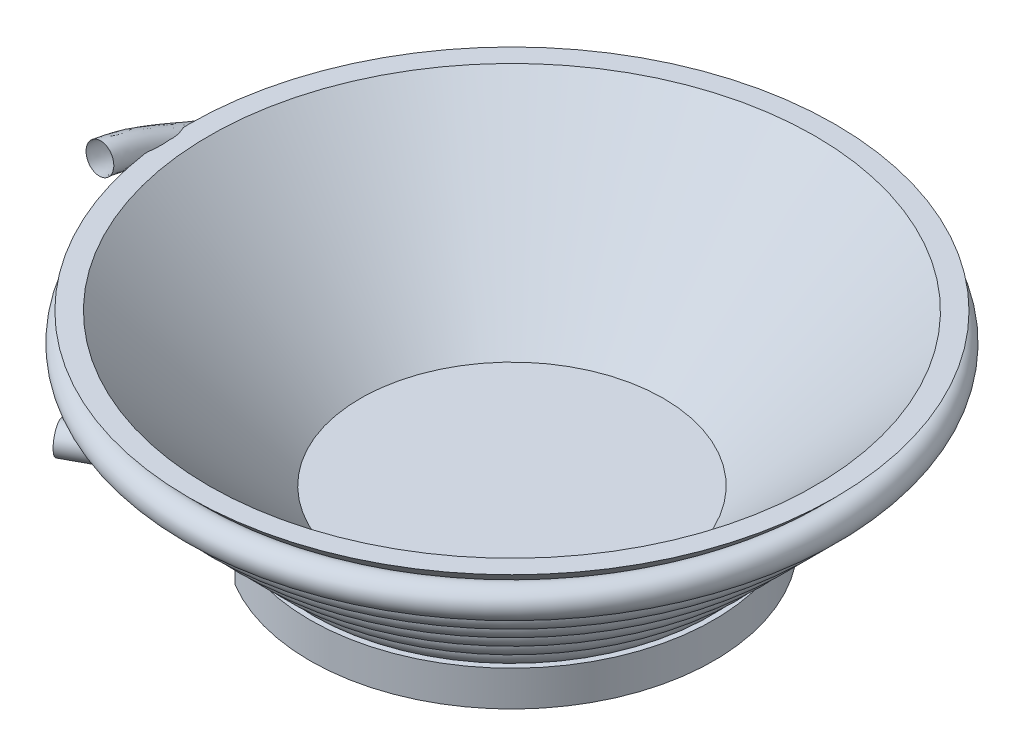
SolidWorks part; units mm, degrees
ref_plane "Plan de face" through (0, 0, 0) normal (0, 0, 1) x (1, 0, 0)
ref_plane "Plan de dessus" through (0, 0, 0) normal (0, 1, 0) x (1, 0, 0)
ref_plane "Plan de droite" through (0, 0, 0) normal (1, 0, 0) x (0, 0, -1)
sketch "Esquisse1" plane through (0, 0, 0) normal (0, 0, 1) x (1, 0, 0)
  line L0 (0, 0) -> (-60, 0)
  line L1 (-60, 0) -> (-120, 60)
  line L2 (-120, 60) -> (-128, 60)
  line L3 (-128, 60) -> (-68, 0)
  line L4 (-68, 0) -> (-68, -6)
  line L5 (-68, -6) -> (-80, -6)
  line L6 (-80, -6) -> (-80, -20)
  line L7 (-80, -20) -> (0, -20)
  line L8 (0, -20) -> (0, 0)
  line L9 (-136.4942, 60.716) -> (-68, -7.7782) construction
  point P3 (-71.3843, -20)
  dimension "D1" = 60
  dimension "D2" = 60
  dimension "D3" = 45
  dimension "D4" = 8
  dimension "D5" = 20
  dimension "D6" = 6
  dimension "D7" = 5.5
  dimension "D8" = 80
revolve "Révolution1" add sketch "Esquisse1" angle 360 about L8
sketch "Esquisse2" plane through (0, 0, 0) normal (0, 0, 1) x (1, 0, 0)
  line L0 (-136.4942, 60.716) -> (-68, -7.7782) construction
  line L1 (-136.4942, 60.716) -> (-68, -7.7782)
surface "Surface-Révolution1" sketch "Esquisse2" parameters "D1"=360
sketch "Esquisse3" plane through (0, 0, 0) normal (1, 0, 0) x (0, 0, -1)
  line L0 (136.4942, 60.716) -> (-136.4942, 60.716) construction
  line L1 (30, -30) -> (-30, -30)
  line L2 (30, -30) -> (30, 70.716)
  line L3 (30, 70.716) -> (-30, 70.716)
  line L4 (-30, -30) -> (-30, 70.716)
  line L5 (30, -30) -> (-30, 70.716) construction
  line L6 (30, 70.716) -> (-30, -30) construction
  line L7 (-80, -20) -> (80, -20) construction
  point P0 (0, 20.358)
  dimension "D1" = 10
  dimension "D2" = 10
  dimension "D3" = 60
surface "Surface-Restreindre1"
ref_plane "Plan7" through (0, -1, 0) normal (0, 1, 0) x (1, 0, 0)
ref_plane "Plan8" through (0, 9, 0) normal (0, 1, 0) x (1, 0, 0)
ref_plane "Plan9" through (0, 19, 0) normal (0, 1, 0) x (1, 0, 0)
ref_plane "Plan10" through (0, 29, 0) normal (0, 1, 0) x (1, 0, 0)
ref_plane "Plan11" through (0, 39, 0) normal (0, 1, 0) x (1, 0, 0)
ref_plane "Plan12" through (0, 49, 0) normal (0, 1, 0) x (1, 0, 0)
sketch3d "Esquisse3D1"
  line L0 (-69.9921, -1, 36.5125) -> (-87.7229, -1.2533, 45.7621) construction
  line L1 (-75.151, -1, -14.8065) -> (-61.3923, -1, -46.2204) construction
  line L2 (-75.1897, 9, 40.8446) -> (-87.5144, 9, 8.2695) construction
  line L3 (-51.7152, -1, 54.0122) -> (-69.9921, -1, 36.5125) construction
  line L4 (-87.7229, -11.2541, 45.7621) -> (-117.805, -11.6839, 61.4549)
  arc A0 (-121.1181, 49, 30) -> (-121.1181, 49, -30) centre (0, 49, 0) ccw
  arc A1 (-121.1181, 49, 30) -> (-121.1181, 49, -30) centre (0, 49, 0) ccw
  arc A2 (-110.7881, 39, 30.0003) -> (-110.7881, 39, -30.0003) centre (0, 39, 0) ccw
  arc A3 (-110.7881, 39, 30.0003) -> (-110.7881, 39, -30.0003) centre (0, 39, 0) ccw
  arc A4 (-100.3916, 29, 30) -> (-100.3916, 29, -30) centre (0, 29, 0) ccw
  arc A5 (-100.3916, 29, 30) -> (-100.3916, 29, -30) centre (0, 29, 0) ccw
  arc A6 (-89.905, 19, 30) -> (-89.905, 19, -30) centre (0, 19, 0) ccw
  arc A7 (-89.905, 19, 30) -> (-89.905, 19, -30) centre (0, 19, 0) ccw
  arc A8 (-79.2927, 9, 30.0001) -> (-79.2927, 9, -30.0001) centre (0, 9, 0) ccw
  arc A9 (-79.2927, 9, 30.0001) -> (-79.2927, 9, -30.0001) centre (0, 9, 0) ccw
  arc A10 (-68.4965, -1, 30.0001) -> (-68.4965, -1, -30.0001) centre (0, -1, 0) ccw
  arc A11 (-51.7152, -1, 54.0122) -> (-68.4965, -1, -30.0001) centre (0, -1, 0) ccw
  spline S0 degree 3 poles (-68.4965, -1, -30.0001) (-79.1948, -1, -5.5735) (-88.7291, 9, 5.0588) (-79.2927, 9, 30.0001) knots 0 0 0 0 1 1 1 1
  spline S1 degree 3 poles (-79.2927, 9, -30.0001) (-88.7291, 9, -5.0588) (-98.3457, 19, 4.7045) (-89.905, 19, 30) knots 0 0 0 0 1 1 1 1
  spline S2 degree 3 poles (-89.905, 19, -30) (-98.3457, 19, -4.7045) (-108.0267, 29, 4.4498) (-100.3916, 29, 30) knots 0 0 0 0 1 1 1 1
  spline S3 degree 3 poles (-100.3916, 29, -30) (-108.0267, 29, -4.4498) (-117.7582, 39, 4.2606) (-110.7881, 39, 30.0003) knots 0 0 0 0 1 1 1 1
  spline S4 degree 3 poles (-110.7881, 39, -30.0003) (-117.7582, 39, -4.2606) (-127.5295, 49, 4.1155) (-121.1181, 49, 30) knots 0 0 0 0 1 1 1 1
  spline S5 degree 3 poles (-121.1181, 49, -30) (-127.5295, 49, -4.1155) (-132.2364, 59.1359, 10.4404) (-133.1565, 60.716, 30.0001) knots 0 0 0 0 1 1 1 1
  spline S6 degree 3 poles (-51.7152, -1, 54.0122) (-57.0824, -1, 48.8732) (-74.4848, -11.065, 38.8562) (-87.7229, -11.2541, 45.7621) knots 0 0 0 0 1 1 1 1
  point P3 (0, 173.7782, 0)
  point P4 (0, 173.7782, 0)
  point P8 (0, 153.7782, 0)
  point P9 (0, 153.7782, 0)
  point P13 (0, 133.7782, 0)
  point P14 (0, 133.7782, 0)
  point P18 (0, 113.7782, 0)
  point P19 (0, 113.7782, 0)
  point P23 (0, 93.7782, 0)
  point P24 (0, 93.7782, 0)
  point P28 (0, 73.7782, 0)
  point P29 (0, 73.7782, 0)
  point P35 (0, 0, 0)
  point P38 (0, 0, 0)
surface "Surface-Balayage1" parameters "D2"=11.5
sketch "Esquisse8" plane through (0, -6, 0) normal (0, 1, 0) x (1, 0, 0)
  line L0 (-79.7812, 5.9131) -> (-40.798, -68.8151)
  line L5 (-40.798, -68.8151) -> (-98.3134, -98.819)
  line L6 (-98.3134, -98.819) -> (-137.2966, -24.0907)
  line L7 (-137.2966, -24.0907) -> (-79.7812, 5.9131)
  circle A2 centre (0, 0) radius 68 construction
  circle A3 centre (0, 0) radius 80 construction
  point P2 (-117.805, -61.4549)
  point P8 (-79.8857, 4.2757)
  point P11 (-40.6032, -68.9303)
extrude "Enlèv. mat.-Extru.1" cut sketch "Esquisse8" against normal through all
equation "\"D2@Esquisse3D1\"=\"D1@Esquisse3D1\""
equation "\"D3@Esquisse3D1\"=\"D1@Esquisse3D1\""
equation "\"D4@Esquisse3D1\"=\"D1@Esquisse3D1\""
equation "\"D5@Esquisse3D1\"=\"D1@Esquisse3D1\""
equation "\"D6@Esquisse3D1\"=\"D1@Esquisse3D1\""
equation "\"D7@Esquisse3D1\"=\"D1@Esquisse3D1\""
equation "\"D8@Esquisse3D1\"=\"D1@Esquisse3D1\""
equation "\"D9@Esquisse3D1\"=\"D1@Esquisse3D1\""
equation "\"D10@Esquisse3D1\"=\"D1@Esquisse3D1\""
equation "\"D11@Esquisse3D1\"=\"D1@Esquisse3D1\""
